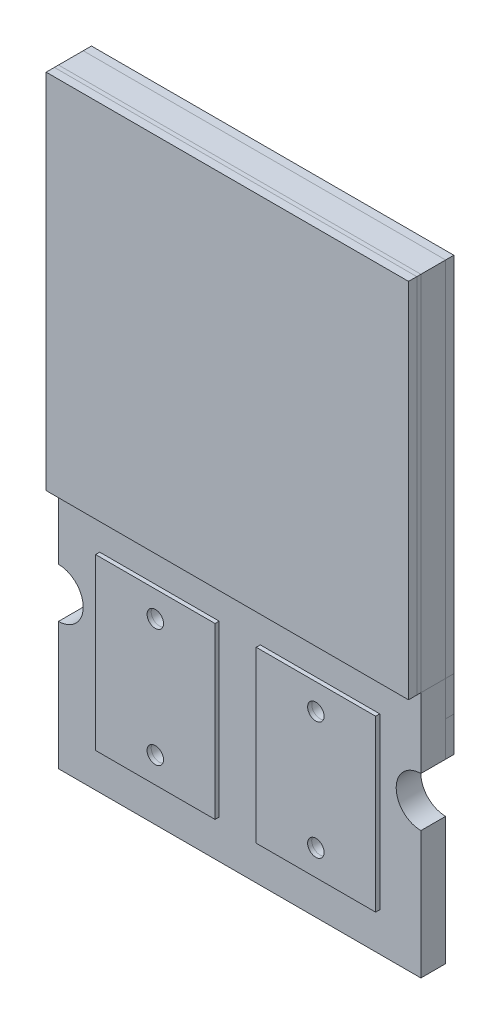
SolidWorks part; units mm, degrees
ref_plane "Ebene vorne" through (0, 0, 0) normal (0, 0, 1) x (1, 0, 0)
ref_plane "Ebene oben" through (0, 0, 0) normal (0, 1, 0) x (1, 0, 0)
ref_plane "Ebene rechts" through (0, 0, 0) normal (1, 0, 0) x (0, 0, -1)
sketch "Model" plane through (0, 0, 0) normal (0, 0, 1) x (1, 0, 0)
  line L0 (13.341, -1.8) -> (13.3407, -3) construction
  line L1 (13.3407, -3) -> (11.891, -3) construction
  line L2 (11.891, -3) -> (11.891, -1.8) construction
  line L3 (11.891, -1.8) -> (13.341, -1.8) construction
  line L4 (11.391, -1.8) -> (11.391, -3) construction
  line L5 (11.391, -3) -> (9.9414, -3) construction
  line L6 (9.9414, -3) -> (9.9414, -1.8) construction
  line L7 (9.9414, -1.8) -> (11.391, -1.8) construction
  line L8 (13.8408, 0) -> (13.8408, 4.4) construction
  line L9 (13.8408, 4.4) -> (9.4408, 4.4) construction
  line L10 (9.4408, 4.4) -> (9.4408, 0) construction
  line L11 (9.4408, 0) -> (9.4406, -0.85) construction
  line L12 (9.4406, -1.45) -> (9.4406, -3) construction
  line L13 (9.4406, -3) -> (13.8406, -3) construction
  line L14 (13.8406, -3) -> (13.8406, -1.45) construction
  line L15 (13.8406, -0.85) -> (13.8408, 0) construction
  line L16 (9.74, -1.13) -> (13.5413, -1.13) construction
  line L17 (4.4001, 0) -> (4.4001, 4.4)
  line L18 (4.4001, 4.4) -> (0.0001, 4.4)
  line L19 (0.0001, 4.4) -> (0, 0)
  line L20 (0, 0) -> (0, -0.85)
  line L21 (0, -1.45) -> (0, -3)
  line L22 (0, -3) -> (4.4, -3)
  line L23 (4.4, -3) -> (4.4, -1.45)
  line L24 (4.4, -0.85) -> (4.4001, 0)
  line L25 (0, 0) -> (4.4001, 0)
  line L26 (3.9, -0.5) -> (3.9, -2.5) construction
  line L27 (3.9, -2.5) -> (2.4504, -2.5) construction
  line L28 (2.4504, -2.5) -> (2.4504, -0.5) construction
  line L29 (2.4504, -0.5) -> (3.9, -0.5) construction
  line L30 (1.9504, -0.5) -> (1.9504, -2.5) construction
  line L31 (1.9504, -2.5) -> (0.5, -2.5) construction
  line L32 (0.5, -2.5) -> (0.5, -0.5) construction
  line L33 (0.5, -0.5) -> (1.9504, -0.5) construction
  arc A0 (9.4406, -1.45) -> (9.4406, -0.85) centre (9.4406, -1.15) ccw construction
  arc A1 (13.8406, -0.85) -> (13.8406, -1.45) centre (13.8406, -1.15) ccw construction
  arc A2 (0, -1.45) -> (0, -0.85) centre (0, -1.15) ccw
  arc A3 (4.4, -0.85) -> (4.4, -1.45) centre (4.4, -1.15) ccw
extrude "Boss-Extrude1" add sketch "Model" along normal blind 0.3 contours L19 L25 L17 L18 | A3 L24 L25 L20 A2 L21 L22 L23
sketch "Sketch2" plane through (0, 0, 0) normal (0, 0, -1) x (-1, 0, 0)
  line L0 (-0.4998, -1.8004) -> (-0.4998, -3)
  line L1 (-0.4998, -3) -> (-1.9498, -3)
  line L2 (-1.9498, -3) -> (-1.9498, -1.8004)
  line L3 (-1.9498, -1.8004) -> (-0.4998, -1.8004)
  line L4 (-2.4498, -1.8) -> (-2.4498, -3)
  line L5 (-2.4498, -3) -> (-3.8994, -3)
  line L6 (-3.8994, -3) -> (-3.8994, -1.8)
  line L7 (-3.8994, -1.8) -> (-2.4498, -1.8)
  line L8 (0, 0) -> (0, 4.4)
  line L9 (0, 4.4) -> (-4.4, 4.4)
  line L10 (-4.4, 4.4) -> (-4.4, 0)
  line L11 (-4.4, 0) -> (-4.4001, -0.85)
  line L12 (-4.4001, -1.45) -> (-4.4001, -3)
  line L13 (-4.4001, -3) -> (-0.0001, -3)
  line L14 (-0.0001, -3) -> (-0.0001, -1.45)
  line L15 (-0.0001, -0.85) -> (0, 0)
  line L16 (-4.1008, -1.13) -> (-0.2995, -1.13)
  arc A0 (-4.4001, -1.45) -> (-4.4001, -0.85) centre (-4.4001, -1.15) ccw
  arc A1 (-0.0001, -0.85) -> (-0.0001, -1.45) centre (-0.0001, -1.15) ccw
  line M1 (0, 0) -> (-0.0001, 4.4)
  line M2 (-0.0001, 4.4) -> (-4.4001, 4.4)
  line M4 (-4.4001, 0) -> (-4.4, -0.85)
  arc M5 (-4.4, -0.85) -> (-4.4, -1.45) centre (-4.4, -1.15) cw
  line M7 (-4.4, -3) -> (0, -3)
extrude "Boss-Extrude2" add sketch "Sketch2" along normal blind 0.05 separate body contours A1 L15 L10 L11 L16 M1 M2 M4 M5 | L7 L6 L4 M7 | L3 L2 L0 M7
sketch "Sketch3" plane through (0, 0, -0.05) normal (0, 0, -1) x (-1, 0, 0)
  line L7 (-0.0001, -0.85) -> (0, 0)
  line L8 (0, 0) -> (-0.0001, 4.4)
  line L9 (-0.0001, 4.4) -> (-4.4, 4.4)
  line L10 (-4.4, 4.4) -> (-4.4, 0)
  line L11 (-4.4, 0) -> (-4.4001, -0.425)
  line L12 (-4.4001, -0.425) -> (-4.4, -0.85)
  line L13 (-4.1007, -1.13) -> (-0.2995, -1.13)
  line L14 (-0.0001, -0.85) -> (0, 0)
  line L15 (0, 0) -> (-0.0001, 4.4)
  line L16 (-0.0001, 4.4) -> (-4.4, 4.4)
  line L17 (-4.4, 4.4) -> (-4.4, 0)
  line L18 (-4.4, 0) -> (-4.4001, -0.425)
  line L19 (-4.4001, -0.425) -> (-4.4, -0.85)
  line L20 (-4.1007, -1.13) -> (-0.2995, -1.13)
  arc A2 (-0.0001, -0.85) -> (-0.2995, -1.13) centre (-0.0001, -1.15) ccw
  arc A3 (-4.1007, -1.13) -> (-4.4, -0.85) centre (-4.4, -1.15) ccw
  arc A4 (-0.0001, -0.85) -> (-0.2995, -1.13) centre (-0.0001, -1.15) ccw
  arc A5 (-4.1007, -1.13) -> (-4.4, -0.85) centre (-4.4, -1.15) ccw
  dimension "D1" = 0
extrude "Boss-Extrude3" add sketch "Sketch3" along normal blind 0.05
sketch "Sketch4" plane through (0, 0, 0.3) normal (0, 0, 1) x (1, 0, 0)
  line L0 (3.9006, -0.4722) -> (3.9006, -2.5324)
  line L1 (3.9006, -2.5324) -> (2.4502, -2.5324)
  line L2 (2.4502, -2.5324) -> (2.4502, -0.4722)
  line L3 (2.4502, -0.4722) -> (3.9006, -0.4722)
  line L4 (1.9502, -0.4722) -> (1.9502, -2.5324)
  line L5 (1.9502, -2.5324) -> (0.5006, -2.5324)
  line L6 (0.5006, -2.5324) -> (0.5006, -0.4722)
  line L7 (0.5006, -0.4722) -> (1.9502, -0.4722)
  line L8 (4.4, 0) -> (4.4, 4.4)
  line L9 (4.4, 4.4) -> (0, 4.4)
  line L10 (0, 4.4) -> (0, 0)
  line L11 (0, 0) -> (-0.0001, -0.85)
  line L12 (-0.0001, -1.45) -> (-0.0001, -3)
  line L13 (-0.0001, -3) -> (4.3999, -3)
  line L14 (4.3999, -3) -> (4.3999, -1.45)
  line L15 (4.3999, -0.85) -> (4.4, 0)
  line L17 (0, 0) -> (4.4, 0)
  arc A0 (-0.0001, -1.45) -> (-0.0001, -0.85) centre (-0.0001, -1.15) ccw
  arc A1 (4.3999, -0.85) -> (4.3999, -1.45) centre (4.3999, -1.15) ccw
  line M1 (0.0001, 4.4) -> (0, 0)
  line M5 (0, -3) -> (4.4, -3)
  line M10 (4.4001, 4.4) -> (0.0001, 4.4)
  dimension "D1" = 2.0602
extrude "Boss-Extrude4" add sketch "Sketch4" along normal blind 0.05 separate body contours L7 L6 L4 M5 | L3 L2 L0 M5 | L17 L8 M1 M10
sketch "Sketch6" plane through (0, 0, 0.35) normal (0, 0, 1) x (1, 0, 0)
  line L1 (0.0001, 4.4) -> (4.4, 4.4)
  line L2 (0.0001, 4.4) -> (0.0001, 0)
  line L3 (0.0001, 0) -> (4.4, 0)
  line L4 (4.4, 4.4) -> (4.4, 0)
extrude "Boss-Extrude5" add sketch "Sketch6" along normal blind 0.1
sketch "Sketch7" plane through (0, 0, 0.35) normal (0, 0, 1) x (1, 0, 0)
  line L0 (1.2254, -0.4722) -> (1.2254, -2.5324) construction
  line L1 (0.5006, -0.4722) -> (1.9502, -0.4722) construction
  line L2 (1.9502, -2.5324) -> (0.5006, -2.5324) construction
  line L3 (0.5006, -1.5023) -> (1.9502, -1.5023) construction
  line L4 (0.5006, -2.5324) -> (0.5006, -0.4722) construction
  line L5 (1.9502, -0.4722) -> (1.9502, -2.5324) construction
  line L6 (2.2001, 0) -> (2.2, -3) construction
  line L7 (0.0001, 0) -> (4.4, 0) construction
  line L8 (0, -3) -> (4.4, -3) construction
  circle A0 centre (1.2254, -0.7861) radius 0.1
  circle A1 centre (1.2254, -2.2185) radius 0.1
  circle A2 centre (3.1746, -2.2185) radius 0.1
  circle A3 centre (3.1747, -0.7862) radius 0.1
  dimension "D1" = 0.2
extrude "Cut-Extrude1" cut sketch "Sketch7" against normal up to surface (0.4 mm away) up to face at (3.1746, -2.4, -0.05)
